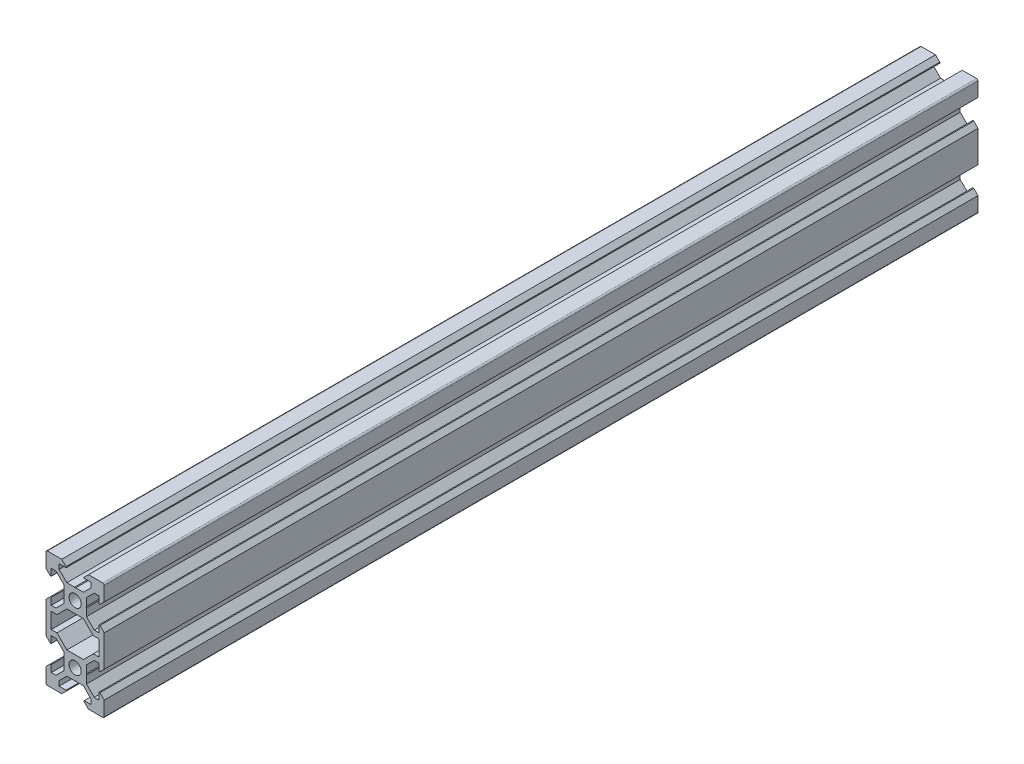
SolidWorks part; units mm, degrees
material "6061-T6 (SS)"
ref_plane "Front Plane" through (0, 0, 0) normal (0, 0, 1) x (1, 0, 0)
ref_plane "Top Plane" through (0, 0, 0) normal (0, 1, 0) x (1, 0, 0)
ref_plane "Right Plane" through (0, 0, 0) normal (1, 0, 0) x (0, 0, -1)
sketch "Sketch1" plane through (0, 0, 0) normal (0, 0, 1) x (1, 0, 0)
  line L0 (0, 0) -> (10, 0) construction
  line L1 (9.5, -20) -> (-9.5, -20)
  line L2 (10, -19.5) -> (10, 19.5)
  line L3 (9.5, 20) -> (-9.5, 20)
  line L4 (-10, -19.5) -> (-10, 19.5)
  line L5 (10, -20) -> (-10, 20) construction
  line L6 (10, 20) -> (-10, -20) construction
  circle A0 centre (0, 10) radius 2.1
  circle A1 centre (0, -10) radius 2.1
  arc A2 (-9.5, -20) -> (-10, -19.5) centre (-9.5, -19.5) cw
  arc A3 (9.5, -20) -> (10, -19.5) centre (9.5, -19.5) ccw
  arc A4 (10, 19.5) -> (9.5, 20) centre (9.5, 19.5) ccw
  arc A5 (-9.5, 20) -> (-10, 19.5) centre (-9.5, 19.5) ccw
  point P0 (0, 0)
  line B0 (0, 10) -> (0, 20) construction
  line B1 (0, 13.69) -> (-0.21, 13.9)
  line B2 (-0.21, 13.9) -> (-2.8393, 13.9)
  line B3 (-2.8393, 13.9) -> (-5.5, 16.5607)
  line B4 (-5.5, 16.5607) -> (-5.5, 18.2)
  line B5 (-5.5, 18.2) -> (-3.125, 18.2)
  line B6 (-3.125, 18.2) -> (-3.125, 18.545)
  line B7 (-3.125, 18.545) -> (-4.58, 20)
  line B8 (-4.58, 20) -> (4.58, 20)
  line B9 (0, 10) -> (-5.9132, 15.9132) construction
  line B10 (3.125, 18.545) -> (4.58, 20)
  line B11 (3.125, 18.2) -> (3.125, 18.545)
  line B12 (5.5, 18.2) -> (3.125, 18.2)
  line B13 (5.5, 16.5607) -> (5.5, 18.2)
  line B14 (2.8393, 13.9) -> (5.5, 16.5607)
  line B15 (0.21, 13.9) -> (2.8393, 13.9)
  line B16 (0, 13.69) -> (0.21, 13.9)
  line B17 (0, 10) -> (-10, 10) construction
  line B18 (-3.69, 10) -> (-3.9, 9.79)
  line B19 (-3.9, 9.79) -> (-3.9, 7.1607)
  line B20 (-3.9, 7.1607) -> (-6.5607, 4.5)
  line B21 (-6.5607, 4.5) -> (-8.2, 4.5)
  line B22 (-8.2, 4.5) -> (-8.2, 6.875)
  line B23 (-8.2, 6.875) -> (-8.545, 6.875)
  line B24 (-8.545, 6.875) -> (-10, 5.42)
  line B25 (-10, 5.42) -> (-10, 14.58)
  line B26 (0, 10) -> (-5.9132, 4.0868) construction
  line B27 (-8.545, 13.125) -> (-10, 14.58)
  line B28 (-8.2, 13.125) -> (-8.545, 13.125)
  line B29 (-8.2, 15.5) -> (-8.2, 13.125)
  line B30 (-6.5607, 15.5) -> (-8.2, 15.5)
  line B31 (-3.9, 12.8393) -> (-6.5607, 15.5)
  line B32 (-3.9, 10.21) -> (-3.9, 12.8393)
  line B33 (-3.69, 10) -> (-3.9, 10.21)
  line B34 (0, -10) -> (-10, -10) construction
  line B35 (-3.69, -10) -> (-3.9, -10.21)
  line B36 (-3.9, -10.21) -> (-3.9, -12.8393)
  line B37 (-3.9, -12.8393) -> (-6.5607, -15.5)
  line B38 (-6.5607, -15.5) -> (-8.2, -15.5)
  line B39 (-8.2, -15.5) -> (-8.2, -13.125)
  line B40 (-8.2, -13.125) -> (-8.545, -13.125)
  line B41 (-8.545, -13.125) -> (-10, -14.58)
  line B42 (-10, -14.58) -> (-10, -5.42)
  line B43 (0, -10) -> (-5.9132, -15.9132) construction
  line B44 (-8.545, -6.875) -> (-10, -5.42)
  line B45 (-8.2, -6.875) -> (-8.545, -6.875)
  line B46 (-8.2, -4.5) -> (-8.2, -6.875)
  line B47 (-6.5607, -4.5) -> (-8.2, -4.5)
  line B48 (-3.9, -7.1607) -> (-6.5607, -4.5)
  line B49 (-3.9, -9.79) -> (-3.9, -7.1607)
  line B50 (-3.69, -10) -> (-3.9, -9.79)
  line B51 (0, -10) -> (0, -20) construction
  line B52 (0, -13.69) -> (0.21, -13.9)
  line B53 (0.21, -13.9) -> (2.8393, -13.9)
  line B54 (2.8393, -13.9) -> (5.5, -16.5607)
  line B55 (5.5, -16.5607) -> (5.5, -18.2)
  line B56 (5.5, -18.2) -> (3.125, -18.2)
  line B57 (3.125, -18.2) -> (3.125, -18.545)
  line B58 (3.125, -18.545) -> (4.58, -20)
  line B59 (4.58, -20) -> (-4.58, -20)
  line B60 (0, -10) -> (5.9132, -15.9132) construction
  line B61 (-3.125, -18.545) -> (-4.58, -20)
  line B62 (-3.125, -18.2) -> (-3.125, -18.545)
  line B63 (-5.5, -18.2) -> (-3.125, -18.2)
  line B64 (-5.5, -16.5607) -> (-5.5, -18.2)
  line B65 (-2.8393, -13.9) -> (-5.5, -16.5607)
  line B66 (-0.21, -13.9) -> (-2.8393, -13.9)
  line B67 (0, -13.69) -> (-0.21, -13.9)
  line B68 (0, -10) -> (10, -10) construction
  line B69 (3.69, -10) -> (3.9, -9.79)
  line B70 (3.9, -9.79) -> (3.9, -7.1607)
  line B71 (3.9, -7.1607) -> (6.5607, -4.5)
  line B72 (6.5607, -4.5) -> (8.2, -4.5)
  line B73 (8.2, -4.5) -> (8.2, -6.875)
  line B74 (8.2, -6.875) -> (8.545, -6.875)
  line B75 (8.545, -6.875) -> (10, -5.42)
  line B76 (10, -5.42) -> (10, -14.58)
  line B77 (0, -10) -> (5.9132, -4.0868) construction
  line B78 (8.545, -13.125) -> (10, -14.58)
  line B79 (8.2, -13.125) -> (8.545, -13.125)
  line B80 (8.2, -15.5) -> (8.2, -13.125)
  line B81 (6.5607, -15.5) -> (8.2, -15.5)
  line B82 (3.9, -12.8393) -> (6.5607, -15.5)
  line B83 (3.9, -10.21) -> (3.9, -12.8393)
  line B84 (3.69, -10) -> (3.9, -10.21)
  line B85 (0, 10) -> (10, 10) construction
  line B86 (3.69, 10) -> (3.9, 10.21)
  line B87 (3.9, 10.21) -> (3.9, 12.8393)
  line B88 (3.9, 12.8393) -> (6.5607, 15.5)
  line B89 (6.5607, 15.5) -> (8.2, 15.5)
  line B90 (8.2, 15.5) -> (8.2, 13.125)
  line B91 (8.2, 13.125) -> (8.545, 13.125)
  line B92 (8.545, 13.125) -> (10, 14.58)
  line B93 (10, 14.58) -> (10, 5.42)
  line B94 (0, 10) -> (5.9132, 15.9132) construction
  line B95 (8.545, 6.875) -> (10, 5.42)
  line B96 (8.2, 6.875) -> (8.545, 6.875)
  line B97 (8.2, 4.5) -> (8.2, 6.875)
  line B98 (6.5607, 4.5) -> (8.2, 4.5)
  line B99 (3.9, 7.1607) -> (6.5607, 4.5)
  line B100 (3.9, 9.79) -> (3.9, 7.1607)
  line B101 (3.69, 10) -> (3.9, 9.79)
  line B102 (-8.2, -2.7) -> (-8.2, 2.7)
  line B103 (-8.2, 2.7) -> (-6.2393, 2.7)
  line B104 (-6.2393, 2.7) -> (-2.8393, 6.1)
  line B105 (-2.8393, 6.1) -> (2.8393, 6.1)
  line B106 (0, 6.1) -> (0, 0) construction
  line B107 (0, 0) -> (-8.2, 0) construction
  line B108 (6.2393, 2.7) -> (2.8393, 6.1)
  line B109 (8.2, 2.7) -> (6.2393, 2.7)
  line B110 (8.2, -2.7) -> (8.2, 2.7)
  line B111 (8.2, -2.7) -> (6.2393, -2.7)
  line B112 (6.2393, -2.7) -> (2.8393, -6.1)
  line B113 (-2.8393, -6.1) -> (2.8393, -6.1)
  line B114 (-6.2393, -2.7) -> (-2.8393, -6.1)
  line B115 (-8.2, -2.7) -> (-6.2393, -2.7)
  line B116 (0, 6.1) -> (0, 10) construction
  line B117 (0, 10) -> (-5.0927, 4.9073) construction
  dimension "D4" = 4.2
  dimension "D5" = 0.5
  dimension "D1" = 20
  dimension "D2" = 40
  dimension "D3" = 20
sketch_block_instance "V Slot 1-4"
sketch_block "V Slot 1" parameters "D1"=10, "D2"=11, "D3"=4.3, "D4"=1.8, "D5"=0.21, "D6"=45, "D7"=9.16, "D8"=1.5, "D9"=6.25
sketch_block_instance "V Slot 1-5"
sketch_block_instance "V Slot 1-6"
sketch_block_instance "V Slot 1-7"
sketch_block_instance "V Slot 1-8"
sketch_block_instance "V Slot 1-9"
sketch_block_instance "Center Cutout 1-1"
sketch_block "Center Cutout 1" parameters "D1"=5.4, "D2"=12.2, "D3"=8.2, "D4"=45, "D5"=10, "D6"=1.5
extrude "Boss-Extrude1" add sketch "Sketch1" along normal blind 300 contours B101 B86 B87 B88 B89 B90 B91 B92 L2 A4 L3 B10 B11 B12 B13 B14 B15 B16 B1 B2 B3 B4 B5 B6 B7 A5 L4 B27 B28 B29 B30 B31 B32 B33 B18 B19 B20 B21 B22 B23 B24 B44 B45 B46 B47 B48 B49 B50 B35
